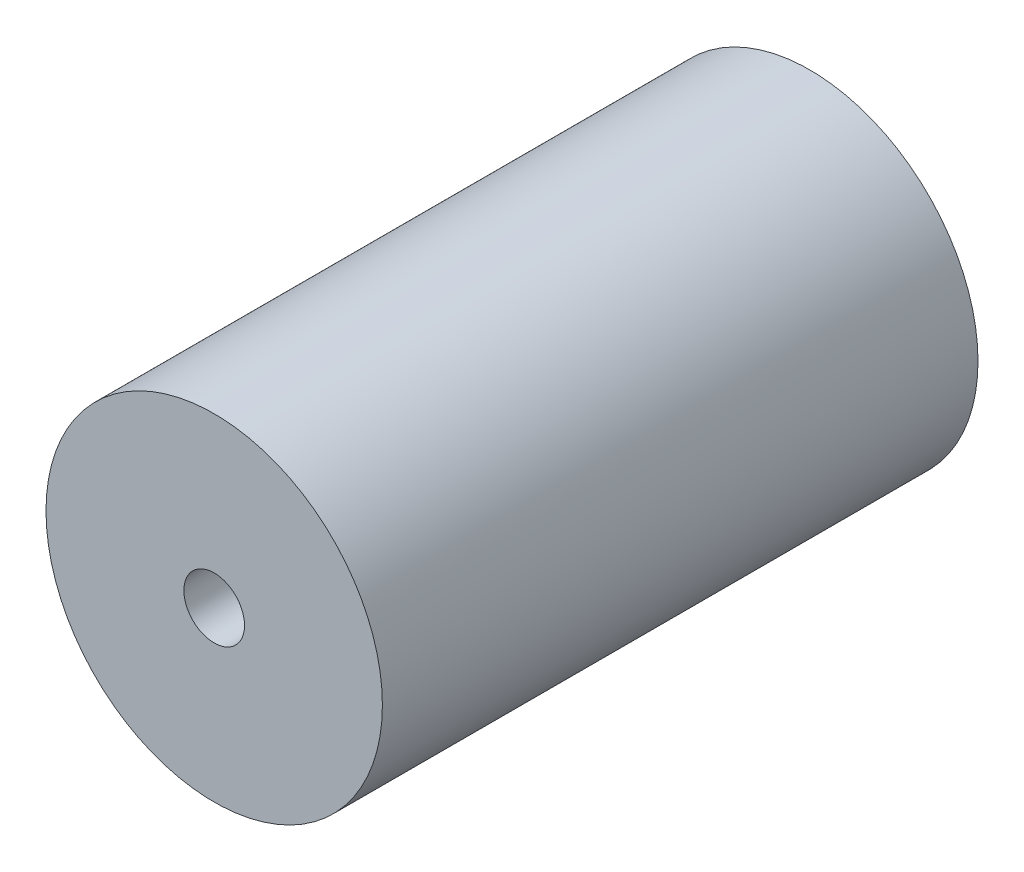
SolidWorks part; units mm, degrees
ref_plane "Front Plane" through (0, 0, 0) normal (0, 0, 1) x (1, 0, 0)
ref_plane "Top Plane" through (0, 0, 0) normal (0, 1, 0) x (1, 0, 0)
ref_plane "Right Plane" through (0, 0, 0) normal (1, 0, 0) x (0, 0, -1)
sketch "Sketch1" plane through (0, 0, 0) normal (0, 0, 1) x (1, 0, 0)
  circle A0 centre (0, 0) radius 30.5
  dimension "D1" = 61
extrude "Boss-Extrude1" add sketch "Sketch1" along normal blind 108
sketch "Sketch2" plane through (0, 0, 0) normal (0, 0, 1) x (1, 0, 0)
  circle A0 centre (0, 0) radius 5.5
  dimension "D1" = 11
extrude "Cut-Extrude1" cut sketch "Sketch2" along normal blind 110
